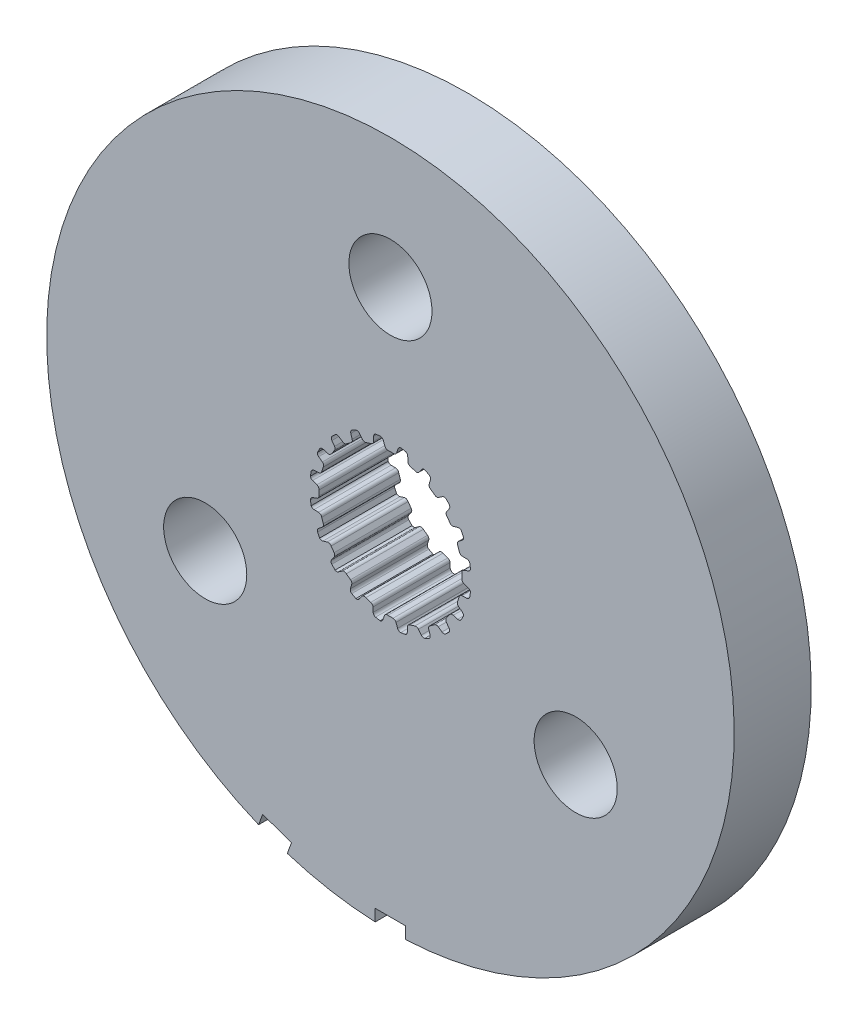
SolidWorks part; units mm, degrees
ref_plane "Front Plane" through (0, 0, 0) normal (0, 0, 1) x (1, 0, 0)
ref_plane "Top Plane" through (0, 0, 0) normal (0, 1, 0) x (1, 0, 0)
ref_plane "Right Plane" through (0, 0, 0) normal (1, 0, 0) x (0, 0, -1)
sketch "Sketch1" plane through (0, 0, 0) normal (0, 0, 1) x (1, 0, 0)
  line L0 (-0.1069, 2.9699) -> (0.1069, 2.9699)
  line L1 (0.3159, 3.2375) -> (0.2537, 3.0575)
  line L2 (-0.2964, 3.2367) -> (-0.2318, 3.0575)
  line L3 (-0.2964, 3.2367) -> (0.3159, 3.2375) construction
  line L4 (0, 3.3252) -> (0, 0) construction
  line L5 (-0.2318, 3.0575) -> (0.2537, 3.0575) construction
  line L6 (-0.4281, 3.3241) -> (0.4281, 3.3263) construction
  line L7 (0.7183, 3.1698) -> (0.7244, 2.9795)
  line L8 (0.816, 2.8576) -> (1.0195, 2.7915)
  line L9 (1.3009, 2.9815) -> (1.1862, 2.8295)
  line L10 (1.6627, 2.7927) -> (1.6097, 2.6099)
  line L11 (1.6591, 2.4655) -> (1.8322, 2.3398)
  line L12 (2.1585, 2.4335) -> (2.0025, 2.3245)
  line L13 (2.4443, 2.1423) -> (2.3374, 1.9847)
  line L14 (2.3398, 1.8322) -> (2.4655, 1.6591)
  line L15 (2.8049, 1.6474) -> (2.6228, 1.5919)
  line L16 (2.9866, 1.2821) -> (2.8363, 1.1653)
  line L17 (2.7915, 1.0195) -> (2.8576, 0.816)
  line L18 (3.1767, 0.7) -> (2.9863, 0.7035)
  line L19 (3.2367, 0.2964) -> (3.0575, 0.2318)
  line L20 (2.9699, 0.1069) -> (2.9699, -0.1069)
  line L21 (3.2375, -0.3159) -> (3.0575, -0.2537)
  line L22 (3.1698, -0.7183) -> (2.9795, -0.7244)
  line L23 (2.8576, -0.816) -> (2.7915, -1.0195)
  line L24 (2.9815, -1.3009) -> (2.8295, -1.1862)
  line L25 (2.7927, -1.6627) -> (2.6099, -1.6097)
  line L26 (2.4655, -1.6591) -> (2.3398, -1.8322)
  line L27 (2.4335, -2.1585) -> (2.3245, -2.0025)
  line L28 (2.1423, -2.4443) -> (1.9847, -2.3374)
  line L29 (1.8322, -2.3398) -> (1.6591, -2.4655)
  line L30 (1.6474, -2.8049) -> (1.5919, -2.6228)
  line L31 (1.2821, -2.9866) -> (1.1653, -2.8363)
  line L32 (1.0195, -2.7915) -> (0.816, -2.8576)
  line L33 (0.7, -3.1767) -> (0.7035, -2.9863)
  line L34 (0.2964, -3.2367) -> (0.2318, -3.0575)
  line L35 (0.1069, -2.9699) -> (-0.1069, -2.9699)
  line L36 (-0.3159, -3.2375) -> (-0.2537, -3.0575)
  line L37 (-0.7183, -3.1698) -> (-0.7244, -2.9795)
  line L38 (-0.816, -2.8576) -> (-1.0195, -2.7915)
  line L39 (-1.3009, -2.9815) -> (-1.1862, -2.8295)
  line L40 (-1.6627, -2.7927) -> (-1.6097, -2.6099)
  line L41 (-1.6591, -2.4655) -> (-1.8322, -2.3398)
  line L42 (-2.1585, -2.4335) -> (-2.0025, -2.3245)
  line L43 (-2.4443, -2.1423) -> (-2.3374, -1.9847)
  line L44 (-2.3398, -1.8322) -> (-2.4655, -1.6591)
  line L45 (-2.8049, -1.6474) -> (-2.6228, -1.5919)
  line L46 (-2.9866, -1.2821) -> (-2.8363, -1.1653)
  line L47 (-2.7915, -1.0195) -> (-2.8576, -0.816)
  line L48 (-3.1767, -0.7) -> (-2.9863, -0.7035)
  line L49 (-3.2367, -0.2964) -> (-3.0575, -0.2318)
  line L50 (-2.9699, -0.1069) -> (-2.9699, 0.1069)
  line L51 (-3.2375, 0.3159) -> (-3.0575, 0.2537)
  line L52 (-3.1698, 0.7183) -> (-2.9795, 0.7244)
  line L53 (-2.8576, 0.816) -> (-2.7915, 1.0195)
  line L54 (-2.9815, 1.3009) -> (-2.8295, 1.1862)
  line L55 (-2.7927, 1.6627) -> (-2.6099, 1.6097)
  line L56 (-2.4655, 1.6591) -> (-2.3398, 1.8322)
  line L57 (-2.4335, 2.1585) -> (-2.3245, 2.0025)
  line L58 (-2.1423, 2.4443) -> (-1.9847, 2.3374)
  line L59 (-1.8322, 2.3398) -> (-1.6591, 2.4655)
  line L60 (-1.6474, 2.8049) -> (-1.5919, 2.6228)
  line L61 (-1.2821, 2.9866) -> (-1.1653, 2.8363)
  line L62 (-1.0195, 2.7915) -> (-0.816, 2.8576)
  line L63 (-0.7, 3.1767) -> (-0.7035, 2.9863)
  line L64 (0.4281, 3.3263) -> (0.62, 3.2938)
  line L65 (1.4351, 3.0312) -> (1.6075, 2.9409)
  line L66 (2.3015, 2.4394) -> (2.4376, 2.3003)
  line L67 (2.9427, 1.6088) -> (3.0291, 1.4344)
  line L68 (3.2958, 0.6207) -> (3.3241, 0.4281)
  line L69 (3.3263, -0.4281) -> (3.2938, -0.62)
  line L70 (3.0312, -1.4351) -> (2.9409, -1.6075)
  line L71 (2.4394, -2.3015) -> (2.3003, -2.4376)
  line L72 (1.6088, -2.9427) -> (1.4344, -3.0291)
  line L73 (0.6207, -3.2958) -> (0.4281, -3.3241)
  line L74 (-0.4281, -3.3263) -> (-0.62, -3.2938)
  line L75 (-1.4351, -3.0312) -> (-1.6075, -2.9409)
  line L76 (-2.3015, -2.4394) -> (-2.4376, -2.3003)
  line L77 (-2.9427, -1.6088) -> (-3.0291, -1.4344)
  line L78 (-3.2958, -0.6207) -> (-3.3241, -0.4281)
  line L79 (-3.3263, 0.4281) -> (-3.2938, 0.62)
  line L80 (-3.0312, 1.4351) -> (-2.9409, 1.6075)
  line L81 (-2.4394, 2.3015) -> (-2.3003, 2.4376)
  line L82 (-1.6088, 2.9427) -> (-1.4344, 3.0291)
  line L83 (-0.6207, 3.2958) -> (-0.4281, 3.3241)
  arc A0 (0.2537, 3.0575) -> (0.1069, 2.9699) centre (0.1283, 3.1009) cw
  arc A1 (-0.2318, 3.0575) -> (-0.1069, 2.9699) centre (-0.1069, 3.1026) ccw
  arc A2 (0.62, 3.2938) -> (0.7183, 3.1698) centre (0.5856, 3.1656) cw
  arc A3 (0.7244, 2.9795) -> (0.816, 2.8576) centre (0.857, 2.9838) ccw
  arc A4 (-0.4281, 3.3241) -> (-0.2964, 3.2367) centre (-0.4213, 3.1916) cw
  arc A5 (0.4281, 3.3263) -> (0.3159, 3.2375) centre (0.4413, 3.1942) ccw
  arc A6 (1.1862, 2.8295) -> (1.0195, 2.7915) centre (1.0802, 2.9095) cw
  arc A7 (1.4351, 3.0312) -> (1.3009, 2.9815) centre (1.4068, 2.9015) ccw
  arc A8 (1.6075, 2.9409) -> (1.6627, 2.7927) centre (1.5352, 2.8297) cw
  arc A9 (1.6097, 2.6099) -> (1.6591, 2.4655) centre (1.7371, 2.5729) ccw
  arc A10 (2.0025, 2.3245) -> (1.8322, 2.3398) centre (1.9264, 2.4332) cw
  arc A11 (2.3015, 2.4394) -> (2.1585, 2.4335) centre (2.2346, 2.3248) ccw
  arc A12 (2.4376, 2.3003) -> (2.4443, 2.1423) centre (2.3345, 2.2168) cw
  arc A13 (2.3374, 1.9847) -> (2.3398, 1.8322) centre (2.4472, 1.9102) ccw
  arc A14 (2.6228, 1.5919) -> (2.4655, 1.6591) centre (2.5841, 1.7189) cw
  arc A15 (2.9427, 1.6088) -> (2.8049, 1.6474) centre (2.8436, 1.5205) ccw
  arc A16 (3.0291, 1.4344) -> (2.9866, 1.2821) centre (2.9052, 1.3869) cw
  arc A17 (2.8363, 1.1653) -> (2.7915, 1.0195) centre (2.9177, 1.0605) ccw
  arc A18 (2.9863, 0.7035) -> (2.8576, 0.816) centre (2.9887, 0.8362) cw
  arc A19 (3.2958, 0.6207) -> (3.1767, 0.7) centre (3.1743, 0.5673) ccw
  arc A20 (3.3241, 0.4281) -> (3.2367, 0.2964) centre (3.1916, 0.4213) cw
  arc A21 (3.0575, 0.2318) -> (2.9699, 0.1069) centre (3.1026, 0.1069) ccw
  arc A22 (3.0575, -0.2537) -> (2.9699, -0.1069) centre (3.1009, -0.1283) cw
  arc A23 (3.3263, -0.4281) -> (3.2375, -0.3159) centre (3.1942, -0.4413) ccw
  arc A24 (3.2938, -0.62) -> (3.1698, -0.7183) centre (3.1656, -0.5856) cw
  arc A25 (2.9795, -0.7244) -> (2.8576, -0.816) centre (2.9838, -0.857) ccw
  arc A26 (2.8295, -1.1862) -> (2.7915, -1.0195) centre (2.9095, -1.0802) cw
  arc A27 (3.0312, -1.4351) -> (2.9815, -1.3009) centre (2.9015, -1.4068) ccw
  arc A28 (2.9409, -1.6075) -> (2.7927, -1.6627) centre (2.8297, -1.5352) cw
  arc A29 (2.6099, -1.6097) -> (2.4655, -1.6591) centre (2.5729, -1.7371) ccw
  arc A30 (2.3245, -2.0025) -> (2.3398, -1.8322) centre (2.4332, -1.9264) cw
  arc A31 (2.4394, -2.3015) -> (2.4335, -2.1585) centre (2.3248, -2.2346) ccw
  arc A32 (2.3003, -2.4376) -> (2.1423, -2.4443) centre (2.2168, -2.3345) cw
  arc A33 (1.9847, -2.3374) -> (1.8322, -2.3398) centre (1.9102, -2.4472) ccw
  arc A34 (1.5919, -2.6228) -> (1.6591, -2.4655) centre (1.7189, -2.5841) cw
  arc A35 (1.6088, -2.9427) -> (1.6474, -2.8049) centre (1.5205, -2.8436) ccw
  arc A36 (1.4344, -3.0291) -> (1.2821, -2.9866) centre (1.3869, -2.9052) cw
  arc A37 (1.1653, -2.8363) -> (1.0195, -2.7915) centre (1.0605, -2.9177) ccw
  arc A38 (0.7035, -2.9863) -> (0.816, -2.8576) centre (0.8362, -2.9887) cw
  arc A39 (0.6207, -3.2958) -> (0.7, -3.1767) centre (0.5673, -3.1743) ccw
  arc A40 (0.4281, -3.3241) -> (0.2964, -3.2367) centre (0.4213, -3.1916) cw
  arc A41 (0.2318, -3.0575) -> (0.1069, -2.9699) centre (0.1069, -3.1026) ccw
  arc A42 (-0.2537, -3.0575) -> (-0.1069, -2.9699) centre (-0.1283, -3.1009) cw
  arc A43 (-0.4281, -3.3263) -> (-0.3159, -3.2375) centre (-0.4413, -3.1942) ccw
  arc A44 (-0.62, -3.2938) -> (-0.7183, -3.1698) centre (-0.5856, -3.1656) cw
  arc A45 (-0.7244, -2.9795) -> (-0.816, -2.8576) centre (-0.857, -2.9838) ccw
  arc A46 (-1.1862, -2.8295) -> (-1.0195, -2.7915) centre (-1.0802, -2.9095) cw
  arc A47 (-1.4351, -3.0312) -> (-1.3009, -2.9815) centre (-1.4068, -2.9015) ccw
  arc A48 (-1.6075, -2.9409) -> (-1.6627, -2.7927) centre (-1.5352, -2.8297) cw
  arc A49 (-1.6097, -2.6099) -> (-1.6591, -2.4655) centre (-1.7371, -2.5729) ccw
  arc A50 (-2.0025, -2.3245) -> (-1.8322, -2.3398) centre (-1.9264, -2.4332) cw
  arc A51 (-2.3015, -2.4394) -> (-2.1585, -2.4335) centre (-2.2346, -2.3248) ccw
  arc A52 (-2.4376, -2.3003) -> (-2.4443, -2.1423) centre (-2.3345, -2.2168) cw
  arc A53 (-2.3374, -1.9847) -> (-2.3398, -1.8322) centre (-2.4472, -1.9102) ccw
  arc A54 (-2.6228, -1.5919) -> (-2.4655, -1.6591) centre (-2.5841, -1.7189) cw
  arc A55 (-2.9427, -1.6088) -> (-2.8049, -1.6474) centre (-2.8436, -1.5205) ccw
  arc A56 (-3.0291, -1.4344) -> (-2.9866, -1.2821) centre (-2.9052, -1.3869) cw
  arc A57 (-2.8363, -1.1653) -> (-2.7915, -1.0195) centre (-2.9177, -1.0605) ccw
  arc A58 (-2.9863, -0.7035) -> (-2.8576, -0.816) centre (-2.9887, -0.8362) cw
  arc A59 (-3.2958, -0.6207) -> (-3.1767, -0.7) centre (-3.1743, -0.5673) ccw
  arc A60 (-3.3241, -0.4281) -> (-3.2367, -0.2964) centre (-3.1916, -0.4213) cw
  arc A61 (-3.0575, -0.2318) -> (-2.9699, -0.1069) centre (-3.1026, -0.1069) ccw
  arc A62 (-3.0575, 0.2537) -> (-2.9699, 0.1069) centre (-3.1009, 0.1283) cw
  arc A63 (-3.3263, 0.4281) -> (-3.2375, 0.3159) centre (-3.1942, 0.4413) ccw
  arc A64 (-3.2938, 0.62) -> (-3.1698, 0.7183) centre (-3.1656, 0.5856) cw
  arc A65 (-2.9795, 0.7244) -> (-2.8576, 0.816) centre (-2.9838, 0.857) ccw
  arc A66 (-2.8295, 1.1862) -> (-2.7915, 1.0195) centre (-2.9095, 1.0802) cw
  arc A67 (-3.0312, 1.4351) -> (-2.9815, 1.3009) centre (-2.9015, 1.4068) ccw
  arc A68 (-2.9409, 1.6075) -> (-2.7927, 1.6627) centre (-2.8297, 1.5352) cw
  arc A69 (-2.6099, 1.6097) -> (-2.4655, 1.6591) centre (-2.5729, 1.7371) ccw
  arc A70 (-2.3245, 2.0025) -> (-2.3398, 1.8322) centre (-2.4332, 1.9264) cw
  arc A71 (-2.4394, 2.3015) -> (-2.4335, 2.1585) centre (-2.3248, 2.2346) ccw
  arc A72 (-2.3003, 2.4376) -> (-2.1423, 2.4443) centre (-2.2168, 2.3345) cw
  arc A73 (-1.9847, 2.3374) -> (-1.8322, 2.3398) centre (-1.9102, 2.4472) ccw
  arc A74 (-1.5919, 2.6228) -> (-1.6591, 2.4655) centre (-1.7189, 2.5841) cw
  arc A75 (-1.6088, 2.9427) -> (-1.6474, 2.8049) centre (-1.5205, 2.8436) ccw
  arc A76 (-1.4344, 3.0291) -> (-1.2821, 2.9866) centre (-1.3869, 2.9052) cw
  arc A77 (-1.1653, 2.8363) -> (-1.0195, 2.7915) centre (-1.0605, 2.9177) ccw
  arc A78 (-0.7035, 2.9863) -> (-0.816, 2.8576) centre (-0.8362, 2.9887) cw
  arc A79 (-0.6207, 3.2958) -> (-0.7, 3.1767) centre (-0.5673, 3.1743) ccw
  circle A80 centre (0, 0) radius 14.2875
  point P14 (0, 2.9699)
  point P247 (0, 0)
  dimension "D4" = 0.1327
  dimension "D8" = 20
  dimension "D9" = 28.575
  dimension "D1" = 2.9699
  dimension "D2" = 0.2139
  dimension "D3" = 0.1904
  dimension "D5" = 0.0877
  dimension "D6" = 0.4855
  dimension "D7" = 0.8563
extrude "Boss-Extrude1" add sketch "Sketch1" along normal blind 3.2004
sketch "Sketch5" plane through (0, 0, 3.2004) normal (0, 0, 1) x (1, 0, 0)
  line L0 (0, 8.89) -> (0, 0) construction
  line L1 (0, 3.3252) -> (0, 0) construction
  circle A0 centre (0, 0) radius 14.2875 construction
  circle A1 centre (0, 8.89) radius 1.7272
  circle A2 centre (7.699, -4.445) radius 1.7272
  circle A3 centre (-7.699, -4.445) radius 1.7272
  point P15 (0, 0)
  dimension "D2" = 3.4544
  dimension "D1" = 8.89
  dimension "D3" = 3
extrude "Cut-Extrude2" cut sketch "Sketch5" against normal up to surface (3.2004 mm away) up to face at (14.2875, 0, 0)
sketch "Sketch7" plane through (0, 0, 3.2004) normal (0, 0, 1) x (1, 0, 0)
  line L0 (-4.8866, -13.4259) -> (0, 0) construction
  line L1 (-4.2899, -13.643) -> (-4.1162, -13.1657)
  line L2 (-4.1162, -13.1657) -> (-5.3096, -12.7313)
  line L3 (-5.3096, -12.7313) -> (-5.4833, -13.2087)
  line L4 (-5.4833, -13.2087) -> (-4.2899, -13.643)
  line L6 (0, -14.2875) -> (0, 0) construction
  line L7 (0.635, -14.2875) -> (0.635, -13.7795)
  line L8 (0.635, -13.7795) -> (-0.635, -13.7795)
  line L9 (-0.635, -13.7795) -> (-0.635, -14.2875)
  line L10 (-0.635, -14.2875) -> (0.635, -14.2875)
  line L11 (0, 3.3252) -> (0, 0) construction
  circle A0 centre (0, 0) radius 14.2875 construction
  circle A3 centre (0, 0) radius 14.2875 construction
  circle A4 centre (0, 0) radius 14.2875 construction
  point P20 (0, 0)
  dimension "D1" = 1.27
  dimension "D2" = 0.508
  dimension "D3" = 20
extrude "Cut-Extrude3" cut sketch "Sketch7" against normal up to surface (3.2004 mm away) up to face at (1.7272, 8.89, 0)
